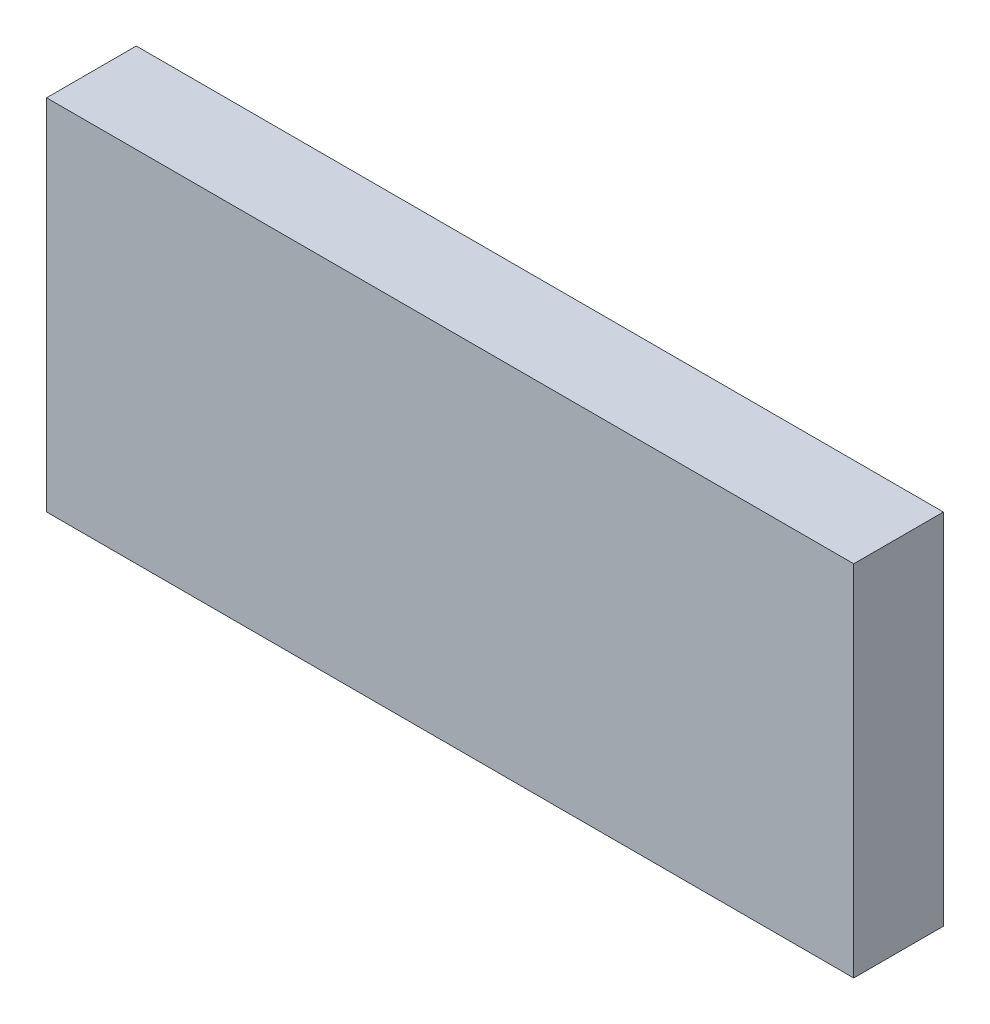
SolidWorks part; units mm, degrees
ref_plane "Front Plane" through (0, 0, 0) normal (0, 0, 1) x (1, 0, 0)
ref_plane "Top Plane" through (0, 0, 0) normal (0, 1, 0) x (1, 0, 0)
ref_plane "Right Plane" through (0, 0, 0) normal (1, 0, 0) x (0, 0, -1)
sketch "Sketch1" plane through (0, 0, 0) normal (0, 0, 1) x (1, 0, 0)
  line L1 (0, 0) -> (22.86, 0)
  line L2 (0, 0) -> (0, 10.16)
  line L3 (0, 10.16) -> (22.86, 10.16)
  line L4 (22.86, 0) -> (22.86, 10.16)
  dimension "D1" = 10.16
  dimension "D2" = 22.86
extrude "Boss-Extrude1" add sketch "Sketch1" along normal blind 2.54 contours L3 L4 L1 L2
